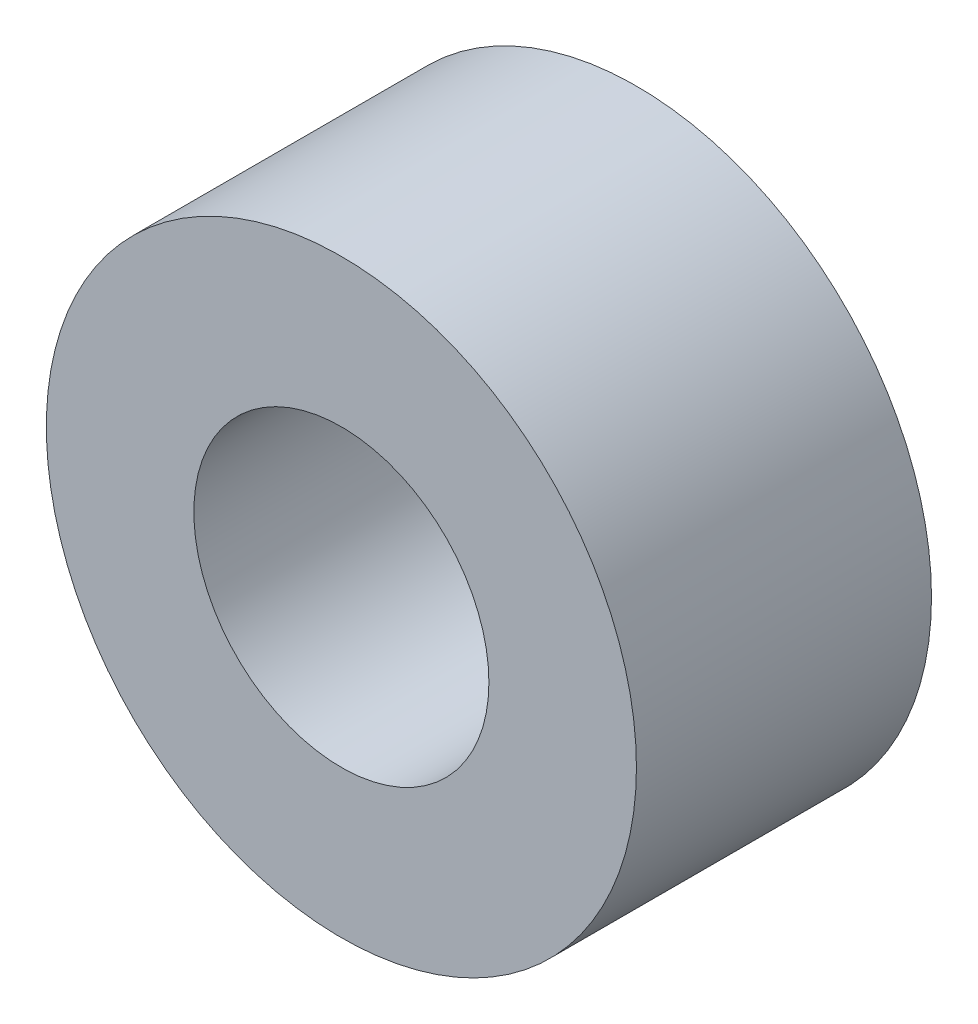
SolidWorks part; units mm, degrees
ref_plane "Front Plane" through (0, 0, 0) normal (0, 0, 1) x (1, 0, 0)
ref_plane "Top Plane" through (0, 0, 0) normal (0, 1, 0) x (1, 0, 0)
ref_plane "Right Plane" through (0, 0, 0) normal (1, 0, 0) x (0, 0, -1)
sketch "Sketch1" plane through (0, 0, 0) normal (0, 0, 1) x (1, 0, 0)
  circle A0 centre (0, 0) radius 5
  dimension "D1" = 10
extrude "Boss-Extrude1" add sketch "Sketch1" along normal blind 5
hole_wizard "Ø5.0mm Dowel Hole1" positions "Sketch2" profile "Sketch3" hole size "Ø5.0" standard "ANSI Metric" end condition up to next
sketch "Sketch2" plane through (0, 0, 5) normal (0, 0, 1) x (1, 0, 0)
  point P0 (0, 0)
sketch "Sketch3" plane through (0, 0, 5) normal (1, 0, 0) x (0, -1, 0)
  line L0 (0, 0) -> (0, 5)
  line L1 (0, 5) -> (2.5, 5)
  line L2 (2.5, 5) -> (2.5, 0)
  line L5 (2.5, 0) -> (0, 0)
  line L11 (0, -6.35) -> (0, 107.95) construction
  dimension "Thru Hole Dia." = 5
  dimension "Thru Hole Depth" = 5
equation "\"Length\"=5"
equation "\"D1@Boss-Extrude1\"=\"Length\""
